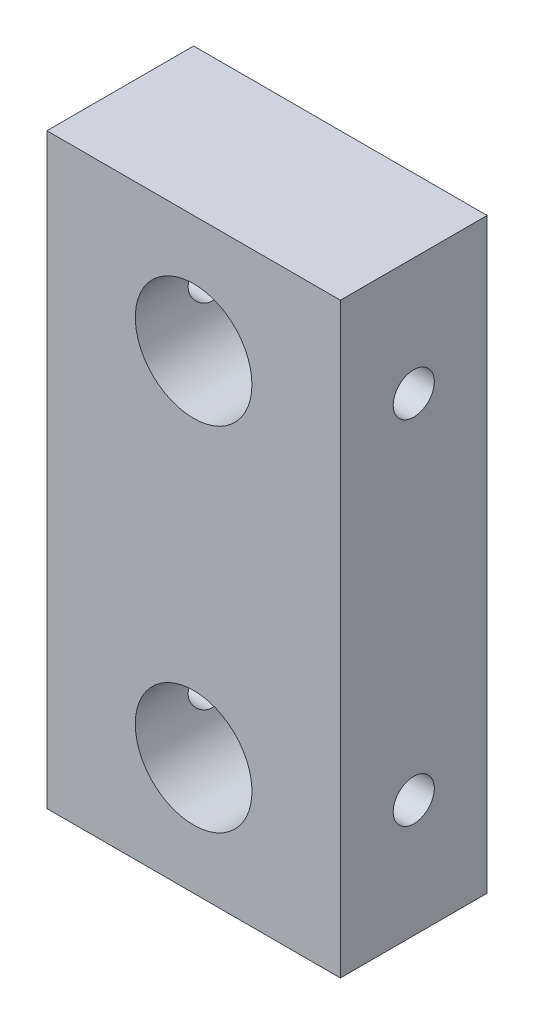
SolidWorks part; units mm, degrees
ref_plane "Plan de face" through (0, 0, 0) normal (0, 0, 1) x (1, 0, 0)
ref_plane "Plan de dessus" through (0, 0, 0) normal (0, 1, 0) x (1, 0, 0)
ref_plane "Plan de droite" through (0, 0, 0) normal (1, 0, 0) x (0, 0, -1)
sketch "Esquisse1" plane through (0, 0, 0) normal (0, 0, 1) x (1, 0, 0)
  line L0 (0, 20) -> (0, -20) construction
  line L1 (-10, -20) -> (10, -20)
  line L2 (-10, -20) -> (-10, 20)
  line L3 (-10, 20) -> (10, 20)
  line L4 (10, -20) -> (10, 20)
  line L5 (-10, -20) -> (10, 20) construction
  line L6 (-10, 20) -> (10, -20) construction
  line L7 (0, 0) -> (10, 0) construction
  circle A0 centre (0, 12) radius 3.9741
  circle A1 centre (0, -12) radius 3.9741
  point P0 (0, 0)
  dimension "D1" = 12
  dimension "D2" = 20
  dimension "D3" = 40
extrude "Boss.-Extru.1" add sketch "Esquisse1" along normal blind 10
sketch "Esquisse2" plane through (-10, 0, 0) normal (-1, 0, 0) x (0, 0, 1)
  line L0 (10, 0) -> (0, 0) construction
  line L1 (10, 20) -> (0, 20) construction
  line L2 (10, 20) -> (10, -20) construction
  line L3 (10, -20) -> (0, -20) construction
  line L4 (0, 20) -> (0, -20) construction
  line L5 (5, 0) -> (5, 20) construction
  circle A0 centre (5, 12) radius 1.4
  circle A1 centre (5, -12) radius 1.4
  dimension "D1" = 12
extrude "Enlèv. mat.-Extru.1" cut sketch "Esquisse2" against normal blind 28
